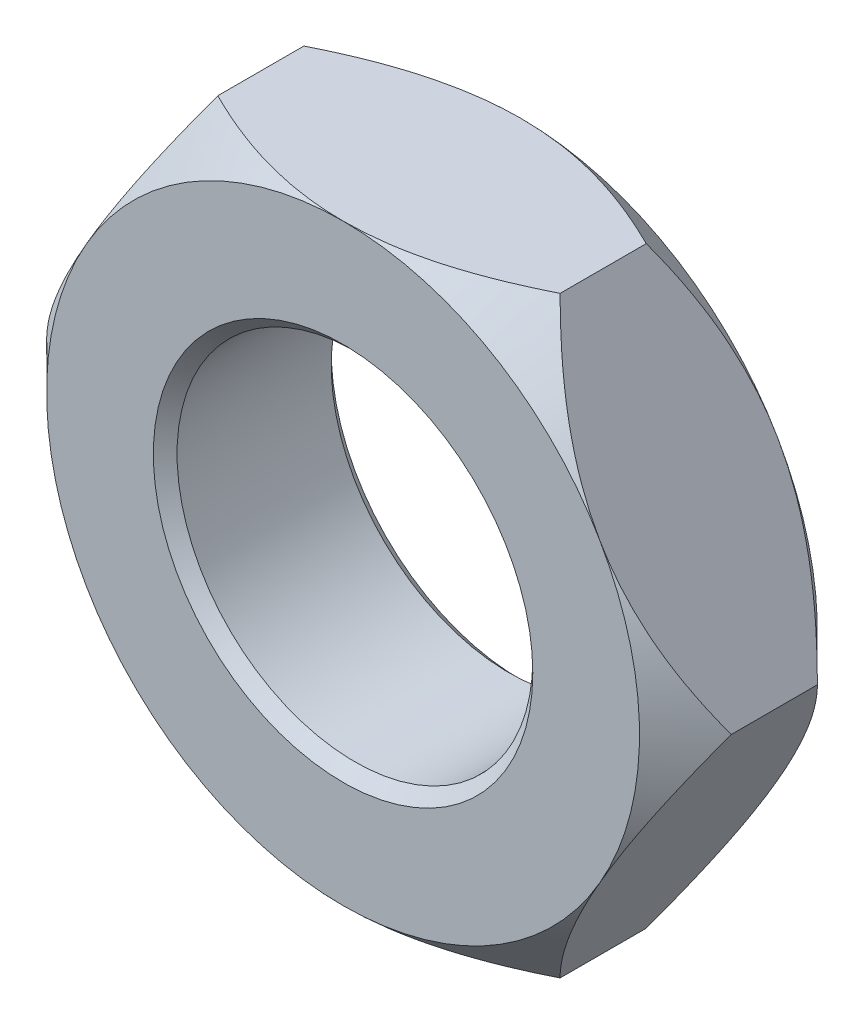
SolidWorks part; units mm, degrees
ref_plane "Спереди" through (0, 0, 0) normal (0, 0, 1) x (1, 0, 0)
ref_plane "Сверху" through (0, 0, 0) normal (0, 1, 0) x (1, 0, 0)
ref_plane "Справа" through (0, 0, 0) normal (1, 0, 0) x (0, 0, -1)
sketch "Эскиз1" plane through (0, 0, 0) normal (0, 0, 1) x (1, 0, 0)
  line L1 (5.7735, 0) -> (2.8868, 5)
  line L2 (2.8868, 5) -> (-2.8868, 5)
  line L3 (-2.8868, 5) -> (-5.7735, 0)
  line L4 (-5.7735, 0) -> (-2.8868, -5)
  line L5 (-2.8868, -5) -> (2.8868, -5)
  line L6 (2.8868, -5) -> (5.7735, 0)
  circle A0 centre (0, 0) radius 3
  circle A1 centre (0, 0) radius 5 construction
extrude "Бобышка-Вытянуть1" add sketch "Эскиз1" along normal blind 3
chamfer "Фаска1" distance 0.2 angle 45 2 edges at (3, 0, 0) (3, 0, 3)
sketch "Эскиз2" plane through (0, 0, 3) normal (0, 0, 1) x (1, 0, 0)
  circle A0 centre (0, 0) radius 5
extrude "Вырез-Вытянуть1" cut sketch "Эскиз2" against normal blind 3 draft 45 flip side to cut
sketch "Эскиз3" plane through (0, 0, 0) normal (0, 0, -1) x (-1, 0, 0)
  circle A0 centre (0, 0) radius 5
extrude "Вырез-Вытянуть2" cut sketch "Эскиз3" against normal blind 3 draft 45 flip side to cut
